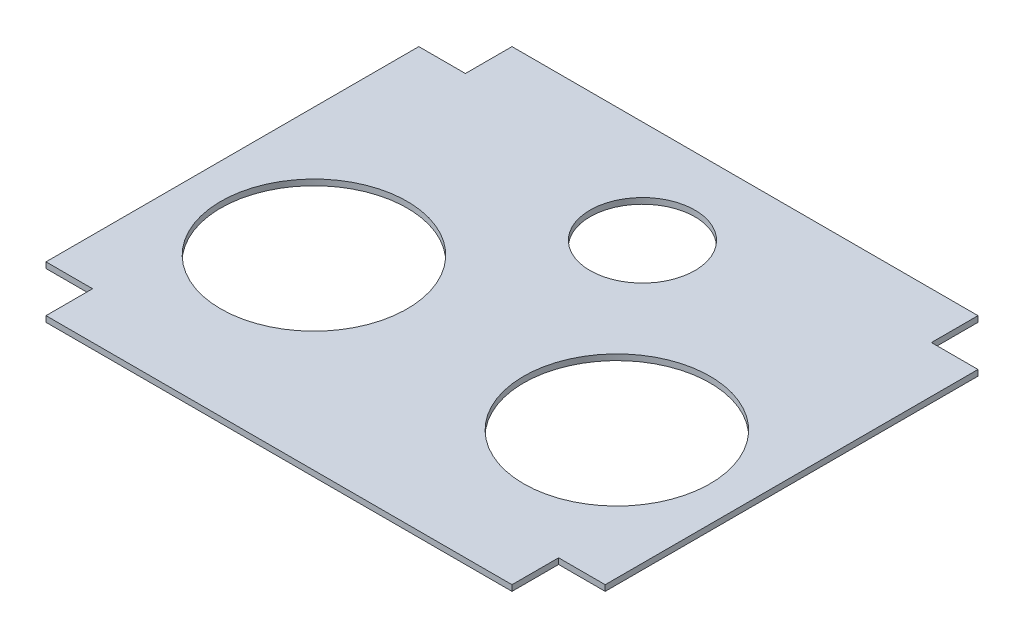
SolidWorks part; units mm, degrees
material "AISI 1020"
ref_plane "Front Plane" through (0, 0, 0) normal (0, 0, 1) x (1, 0, 0)
ref_plane "Top Plane" through (0, 0, 0) normal (0, 1, 0) x (1, 0, 0)
ref_plane "Right Plane" through (0, 0, 0) normal (1, 0, 0) x (0, 0, -1)
sketch "Sketch1" plane through (0, 0, 0) normal (0, 1, 0) x (1, 0, 0)
  line L0 (0, 0) -> (0, -50.8)
  line L1 (0, -50.8) -> (-508, -50.8)
  line L2 (-508, -50.8) -> (-508, 0)
  line L3 (-508, 0) -> (-558.8, 0)
  line L4 (-558.8, 0) -> (-558.8, 406.4)
  line L5 (-558.8, 406.4) -> (-508, 406.4)
  line L6 (-508, 406.4) -> (-508, 457.2)
  line L7 (-508, 457.2) -> (0, 457.2)
  line L8 (0, 457.2) -> (0, 406.4)
  line L9 (0, 406.4) -> (50.8, 406.4)
  line L10 (50.8, 406.4) -> (50.8, 0)
  line L11 (50.8, 0) -> (0, 0)
  line L12 (0, 0) -> (-508, 0) construction
  line L13 (-508, 406.4) -> (-508, 0) construction
  line L14 (-508, 406.4) -> (0, 406.4) construction
  line L15 (0, 406.4) -> (0, 0) construction
  line L16 (-508, -50.8) -> (-508, -76.2) construction
  line L17 (-508, -76.2) -> (0, -76.2) construction
  line L18 (0, -76.2) -> (0, -50.8) construction
  line L20 (-508, 345.4233) -> (0, 345.4233) construction
  line L21 (-419.1, 152.4) -> (-88.9, 152.4) construction
  line L22 (-254, 152.4) -> (-254, 0) construction
  circle A0 centre (-419.1, 152.4) radius 101.6
  circle A1 centre (-419.1, 152.4) radius 171.45 construction
  circle A2 centre (-88.9, 152.4) radius 101.6
  circle A3 centre (-88.9, 152.4) radius 158.75 construction
  circle A4 centre (-254, 345.4233) radius 57.15
  circle A5 centre (-254, 345.4233) radius 82.55 construction
  circle A6 centre (-419.1, 152.4) radius 127 construction
  circle A7 centre (-88.9, 152.4) radius 127 construction
  dimension "D7" = 165.1
  dimension "D8" = 114.3
  dimension "D9" = 203.2
  dimension "D10" = 342.9
  dimension "D11" = 317.5
  dimension "D12" = 203.2
  dimension "D13" = 254
  dimension "D14" = 254
  dimension "D1" = 50.8
  dimension "D2" = 50.8
  dimension "D3" = 50.8
  dimension "D4" = 50.8
  dimension "D5" = 508
  dimension "D6" = 406.4
  dimension "D15" = 25.4
  dimension "D16" = 203.2
extrude "Boss-Extrude1" add sketch "Sketch1" along normal blind 6.35
equation "\"D2@Sketch1\"=\"D1@Sketch1\""
equation "\"D3@Sketch1\"=\"D1@Sketch1\""
equation "\"D4@Sketch1\"=\"D1@Sketch1\""
